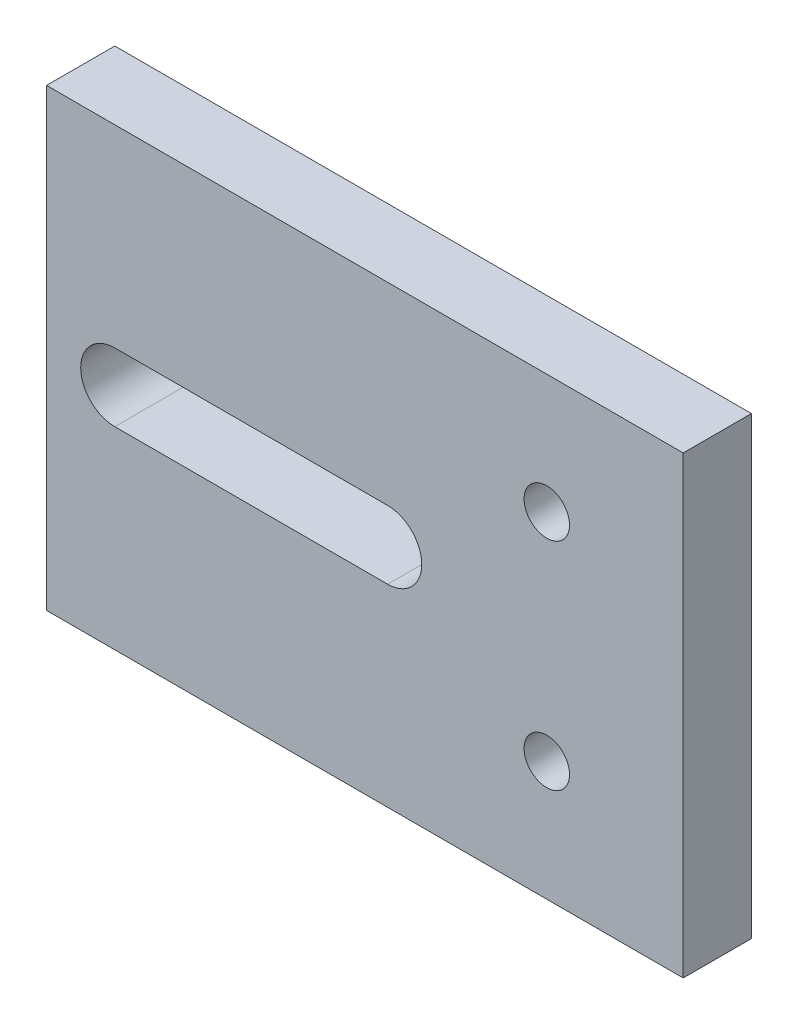
SolidWorks part; units mm, degrees
ref_plane "前视基准面" through (0, 0, 0) normal (0, 0, 1) x (1, 0, 0)
ref_plane "上视基准面" through (0, 0, 0) normal (0, 1, 0) x (1, 0, 0)
ref_plane "右视基准面" through (0, 0, 0) normal (1, 0, 0) x (0, 0, -1)
sketch "草图1" plane through (0, 0, 0) normal (0, 0, 1) x (1, 0, 0)
  line L0 (8, 26.603) -> (8, -19.7616) construction
  line L1 (14, -10) -> (-14, -10)
  line L2 (14, -10) -> (14, 10)
  line L3 (14, 10) -> (-14, 10)
  line L4 (-14, -10) -> (-14, 10)
  line L5 (14, -10) -> (-14, 10) construction
  line L6 (14, 10) -> (-14, -10) construction
  line L7 (-32.389, 0) -> (39.7229, 0) construction
  line L8 (-11, 4.75) -> (1, 4.75) construction
  line L9 (-11, 6.25) -> (1, 6.25)
  line L10 (-11, 3.25) -> (1, 3.25)
  line L11 (-11, -4.75) -> (1, -4.75) construction
  line L12 (-11, -6.25) -> (1, -6.25)
  line L13 (-11, -3.25) -> (1, -3.25)
  circle A0 centre (8, 4.75) radius 1
  circle A1 centre (8, -4.75) radius 1
  arc A2 (-11, 6.25) -> (-11, 3.25) centre (-11, 4.75) ccw
  arc A3 (1, 3.25) -> (1, 6.25) centre (1, 4.75) ccw
  arc A4 (-11, -6.25) -> (-11, -3.25) centre (-11, -4.75) cw
  arc A5 (1, -3.25) -> (1, -6.25) centre (1, -4.75) cw
  point P0 (0, 0)
  point P14 (-5, 4.75)
  point P23 (-5, -4.75)
  point P28 (8, -4.75)
  dimension "D3" = 2
  dimension "D4" = 2
  dimension "D5" = 9.5
  dimension "D6" = 6
  dimension "D7" = 1.5
  dimension "D8" = 3
  dimension "D9" = 12
  dimension "D10" = 9.5
  dimension "D1" = 20
  dimension "D2" = 28
extrude "凸台-拉伸1" add sketch "草图1" along normal blind 3
sketch "草图2" plane through (0, 0, 3) normal (0, 0, 1) x (1, 0, 0)
  line L0 (1, 0) -> (-11, 0) construction
  line L1 (1, -1.5) -> (-11, -1.5)
  line L2 (1, 1.5) -> (-11, 1.5)
  line L3 (-11, 3.25) -> (1, 3.25) construction
  arc A0 (1, -1.5) -> (1, 1.5) centre (1, 0) ccw
  arc A1 (-11, 1.5) -> (-11, -1.5) centre (-11, 0) ccw
  arc A2 (1, 3.25) -> (1, 6.25) centre (1, 4.75) ccw construction
  point P3 (-5, 0)
  point P11 (2.5, 0)
  point P12 (2.5, 4.75)
extrude "切除-拉伸1" cut sketch "草图2" against normal through all
sketch "草图3" plane through (0, 0, 3) normal (0, 0, 1) x (1, 0, 0)
  line L1 (-13.2325, 7.9382) -> (4.1187, 7.9382)
  line L2 (-13.2325, 7.9382) -> (-13.2325, 2.4874)
  line L3 (-13.2325, 2.4874) -> (4.1187, 2.4874)
  line L4 (4.1187, 7.9382) -> (4.1187, 2.4874)
  line L5 (-13.2325, -2.596) -> (4.4687, -2.596)
  line L6 (-13.2325, -2.596) -> (-13.2325, -7.7209)
  line L7 (-13.2325, -7.7209) -> (4.4687, -7.7209)
  line L8 (4.4687, -2.596) -> (4.4687, -7.7209)
extrude "凸台-拉伸2" add sketch "草图3" against normal up to surface (3 mm away) up to face at (-5, 0, 0)
